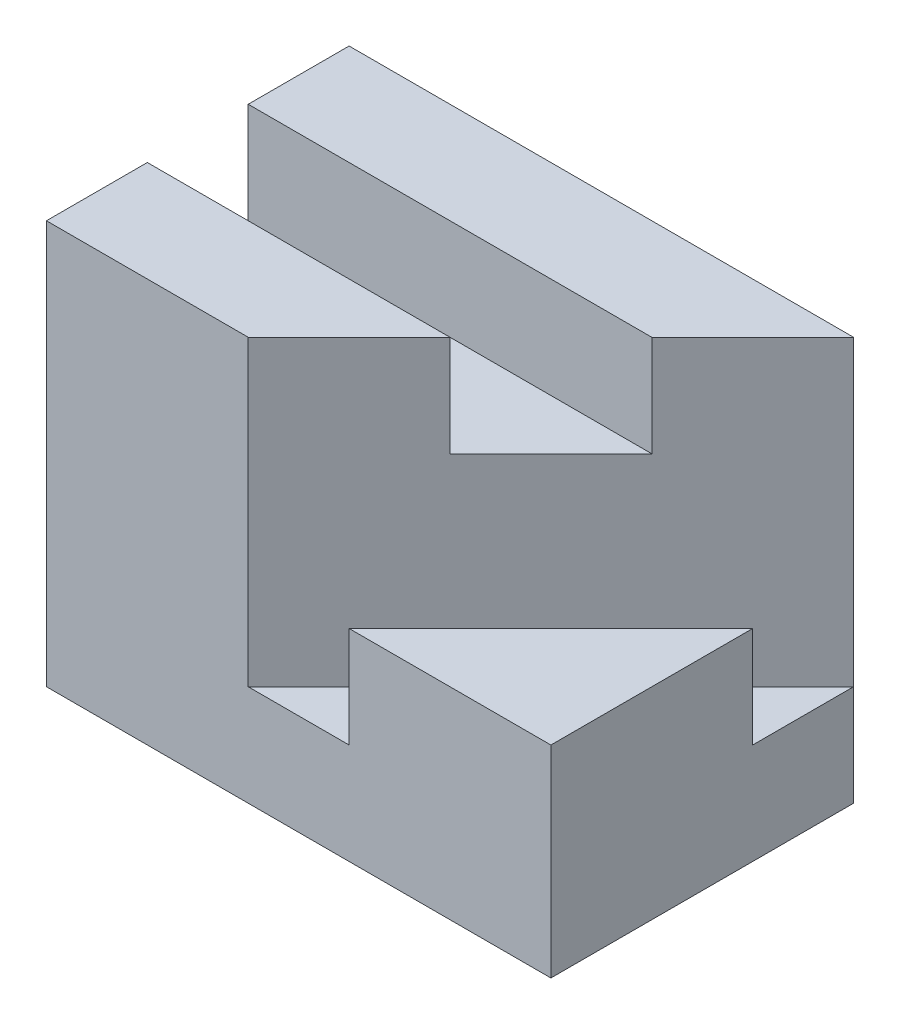
SolidWorks part; units mm, degrees
ref_plane "前基準面" through (0, 0, 0) normal (0, 0, 1) x (1, 0, 0)
ref_plane "上基準面" through (0, 0, 0) normal (0, 1, 0) x (1, 0, 0)
ref_plane "右基準面" through (0, 0, 0) normal (1, 0, 0) x (0, 0, -1)
sketch "草圖1" plane through (0, 0, 0) normal (0, 1, 0) x (1, 0, 0)
  line L1 (-25, -15) -> (25, -15)
  line L2 (-25, -15) -> (-25, 15)
  line L3 (-25, 15) -> (25, 15)
  line L4 (25, -15) -> (25, 15)
  line L5 (-25, -15) -> (25, 15) construction
  line L6 (-25, 15) -> (25, -15) construction
  point P0 (0, 0)
  dimension "D1" = 50
  dimension "D2" = 30
extrude "填料-伸長1" add sketch "草圖1" along normal blind 40
sketch "草圖2" plane through (25, 0, 0) normal (1, 0, 0) x (0, 0, -1)
  line L0 (-15, 40) -> (15, 40) construction
  line L1 (-5, 40) -> (5, 40)
  line L2 (-5, 40) -> (-5, 30)
  line L3 (-5, 30) -> (5, 30)
  line L4 (5, 40) -> (5, 30)
  line L5 (15, 40) -> (15, 0) construction
  line L6 (-15, 40) -> (-15, 0) construction
  dimension "D1" = 10
  dimension "D2" = 10
  dimension "D3" = 10
extrude "除料-伸長1" cut sketch "草圖2" against normal through all
sketch "草圖3" plane through (0, 40, 0) normal (0, 1, 0) x (1, 0, 0)
  line L0 (25, -15) -> (25, 5)
  line L1 (25, 5) -> (5, -15)
  line L2 (-25, -15) -> (25, -15) construction
  line L3 (5, -15) -> (25, -15)
  dimension "D1" = 20
extrude "除料-伸長2" cut sketch "草圖3" against normal blind 20
sketch "草圖4" plane through (0, 40, 0) normal (0, 1, 0) x (1, 0, 0)
  line L0 (25, 15) -> (-5, -15)
  line L1 (-25, -15) -> (5, -15) construction
  line L2 (25, 15) -> (25, 5)
  line L3 (25, 5) -> (5, -15)
  line L4 (5, -15) -> (-5, -15)
  dimension "D1" = 10
extrude "除料-伸長3" cut sketch "草圖4" against normal blind 30
